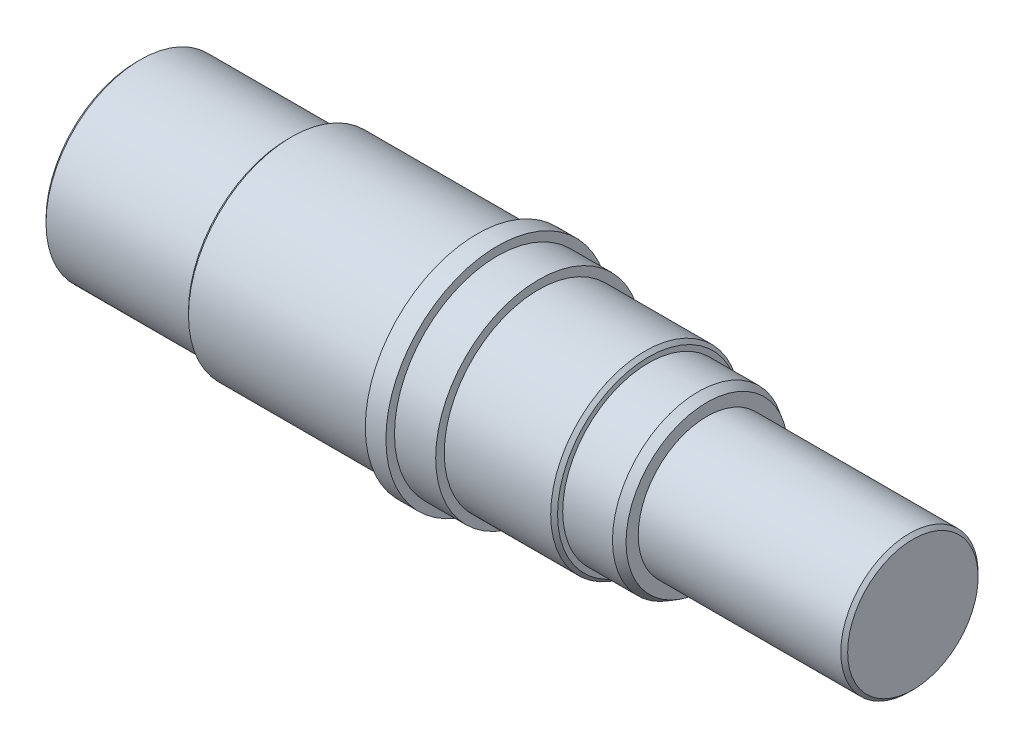
SolidWorks part; units mm, degrees
ref_plane "Ebene vorne" through (0, 0, 0) normal (0, 0, 1) x (1, 0, 0)
ref_plane "Ebene oben" through (0, 0, 0) normal (0, 1, 0) x (1, 0, 0)
ref_plane "Ebene rechts" through (0, 0, 0) normal (1, 0, 0) x (0, 0, -1)
sketch "Skizze1" plane through (0, 0, 0) normal (0, 0, 1) x (1, 0, 0)
  line L0 (17.5895, 0) -> (894.3595, 0) construction
  line L1 (168.1524, 0) -> (168.1524, 26.5)
  line L2 (169.1524, 27.5) -> (184.1524, 27.5)
  line L3 (168.1524, 26.5) -> (169.1524, 27.5)
  line L4 (184.1524, 27.5) -> (212.1524, 27.5)
  line L5 (212.1524, 27.5) -> (212.1524, 29)
  line L6 (213.1524, 30) -> (267.1524, 30)
  line L7 (212.1524, 29) -> (213.1524, 30)
  line L8 (267.1524, 30) -> (267.1524, 32.5)
  line L9 (267.1524, 32.5) -> (273.1524, 32.5)
  line L10 (273.1524, 32.5) -> (273.1524, 30)
  line L11 (273.1524, 30) -> (285.1524, 30)
  line L12 (285.1524, 30) -> (285.1524, 27.5)
  line L13 (285.1524, 27.5) -> (297.6524, 27.5)
  line L14 (297.6524, 27.5) -> (316.1524, 27.5)
  line L15 (297.6524, -28.9351) -> (297.6524, 58.108) construction
  line L16 (317.1524, 26.5) -> (317.1524, 25)
  line L17 (317.1524, 25) -> (331.6524, 25)
  line L18 (316.1524, 27.5) -> (317.1524, 26.5)
  line L19 (334.1524, 23.5566) -> (334.1524, 20)
  line L20 (334.1524, 20) -> (393.1524, 20)
  line L21 (331.6524, 25) -> (334.1524, 23.5566)
  line L22 (394.1524, 19) -> (394.1524, 0)
  line L23 (393.1524, 20) -> (394.1524, 19)
  line L24 (168.1524, 0) -> (394.1524, 0)
  point P4 (168.1524, 27.5)
  point P10 (212.1524, 30)
  point P20 (317.1524, 27.5)
  point P28 (394.1524, 20)
  point P29 (334.1524, 25)
  point P34 (168.1524, 0)
  point P54 (394.1524, 0)
  dimension "D1" = 27.5
  dimension "D2" = 16
  dimension "D3" = 28
  dimension "D4" = 30
  dimension "D5" = 55
  dimension "D8" = 32.5
  dimension "D9" = 6
  dimension "D10" = 30
  dimension "D11" = 27.5
  dimension "D12" = 12.5
  dimension "D13" = 113.5
  dimension "D14" = 19.5
  dimension "D15" = 17
  dimension "D16" = 2.5
  dimension "D18" = 30
  dimension "D19" = 25
  dimension "D20" = 20
  dimension "D21" = 60
  dimension "D22" = 1
  dimension "D23" = 45
revolve "Rotation1" add sketch "Skizze1" angle 360 about L24
